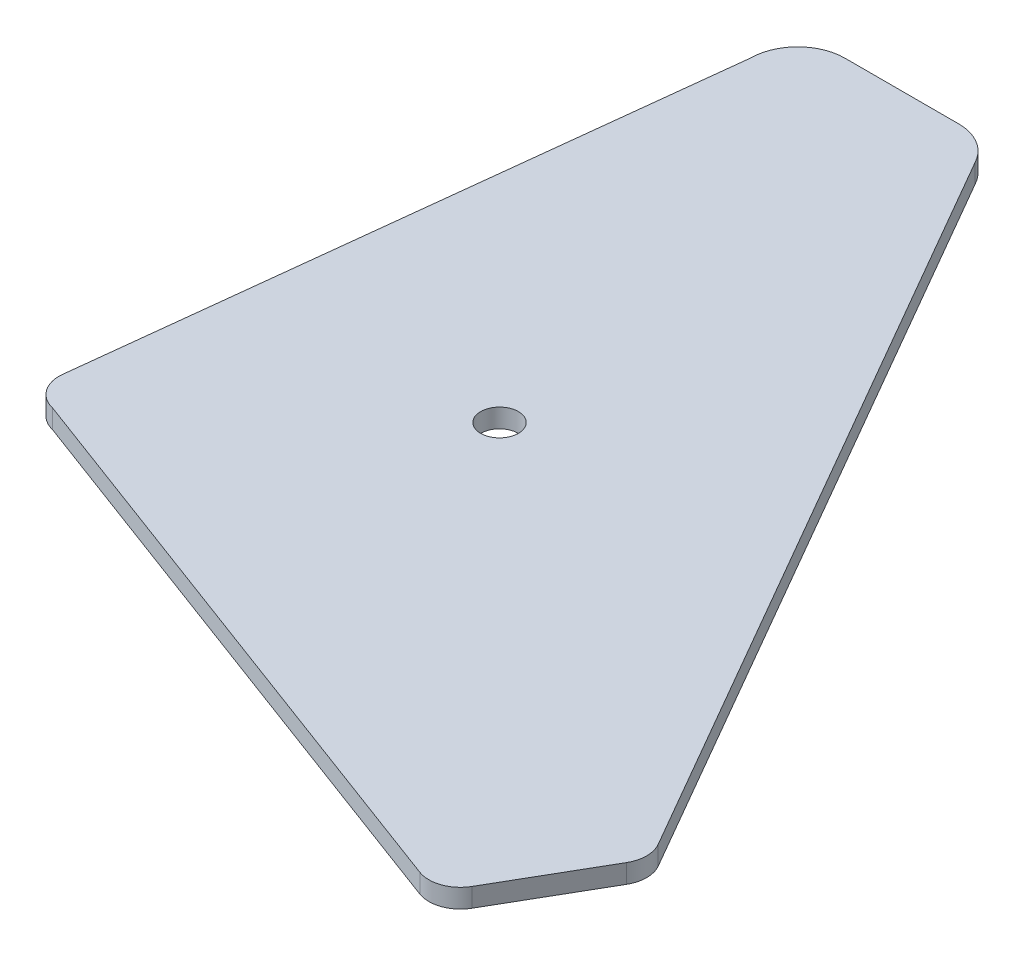
SolidWorks part; units mm, degrees
ref_plane "Front Plane" through (0, 0, 0) normal (0, 0, 1) x (1, 0, 0)
ref_plane "Top Plane" through (0, 0, 0) normal (0, 1, 0) x (1, 0, 0)
ref_plane "Right Plane" through (0, 0, 0) normal (1, 0, 0) x (0, 0, -1)
sketch "Sketch1" plane through (0, 0, 0) normal (0, -1, 0) x (1, 0, 0)
  line L7 (633.5402, -538) -> (596.9413, -538.012)
  line L8 (783.5775, -292.089) -> (646.3169, -530.0109)
  line L11 (753.4104, -246.5514) -> (567.3324, -315.9645)
  line L12 (581.9413, -523.012) -> (559.7091, -326.8192)
  line L15 (765.5641, -250.9179) -> (783.5743, -282.089)
  circle A5 centre (642.331, -382.9399) radius 6
  arc A8 (581.9413, -523.012) -> (596.9413, -538.012) centre (596.9413, -523.012) ccw
  arc A9 (646.3169, -530.0109) -> (633.5402, -538) centre (633.052, -523.0079) cw
  arc A12 (559.7091, -326.8192) -> (567.3324, -315.9645) centre (569.6455, -325.6933) cw
  arc A13 (783.5775, -292.089) -> (783.5743, -282.089) centre (774.9157, -287.0918) ccw
  arc A14 (765.5641, -250.9179) -> (753.4104, -246.5514) centre (756.9055, -255.9208) ccw
  dimension "D1" = 10
  dimension "D2" = 10
  dimension "D3" = 10
  dimension "D4" = 36
  dimension "D5" = 12
  dimension "D6" = 60
  dimension "D7" = 120
  dimension "D8" = 120
extrude "Boss-Extrude1" add sketch "Sketch1" along normal blind 6
